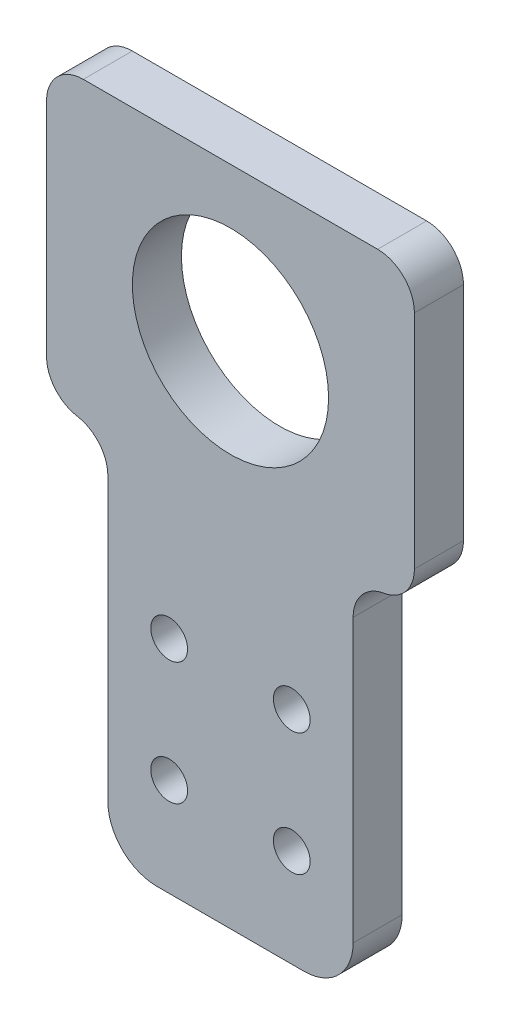
SolidWorks part; units mm, degrees
ref_plane "前视基准面" through (0, 0, 0) normal (0, 0, 1) x (1, 0, 0)
ref_plane "上视基准面" through (0, 0, 0) normal (0, 1, 0) x (1, 0, 0)
ref_plane "右视基准面" through (0, 0, 0) normal (1, 0, 0) x (0, 0, -1)
sketch "草图1" plane through (0, 0, 0) normal (0, 0, 1) x (1, 0, 0)
  line L1 (-10, -15) -> (10, -15)
  line L2 (-10, -15) -> (-10, 15)
  line L3 (-10, 15) -> (10, 15)
  line L4 (10, -15) -> (10, 15)
  line L5 (-10, -15) -> (10, 15) construction
  line L6 (-10, 15) -> (10, -15) construction
  circle A0 centre (-5, 3) radius 1.5
  circle A1 centre (5, 3) radius 1.5
  circle A2 centre (-5, -7) radius 1.5
  circle A3 centre (5, -7) radius 1.5
  point P0 (0, 0)
  dimension "D5" = 3
  dimension "D7" = 3
  dimension "D8" = 3
  dimension "D9" = 3
  dimension "D1" = 10
  dimension "D2" = 20
  dimension "D3" = 30
  dimension "D4" = 10
  dimension "D6" = 10
  dimension "D10" = 5
  dimension "D11" = 8
extrude "凸台-拉伸1" add sketch "草图1" along normal blind 4
sketch "草图2" plane through (0, 15, 0) normal (0, 1, 0) x (1, 0, 0)
  line L1 (-15, 0) -> (15, 0)
  line L2 (-15, 0) -> (-15, -4)
  line L3 (-15, -4) -> (15, -4)
  line L4 (15, 0) -> (15, -4)
  line L5 (-15, 0) -> (15, -4) construction
  line L6 (-15, -4) -> (15, 0) construction
  point P0 (0, -2)
  dimension "D1" = 30
  dimension "D2" = 0
extrude "凸台-拉伸2" add sketch "草图2" along normal blind 24
sketch "草图3" plane through (0, 0, 4) normal (0, 0, 1) x (1, 0, 0)
  line L0 (-15, 39) -> (15, 39) construction
  circle A0 centre (0, 26.5) radius 8
  dimension "D1" = 16
  dimension "D2" = 12.5
fillet "圆角1" radius 3 2 edges at (10, 15, 2) (-10, 15, 2)
extrude "切除-拉伸1" cut sketch "草图3" against normal blind 24
fillet "圆角2" radius 3 4 edges at (15, 15, 2) (15, 39, 2) (-15, 39, 2) (-15, 15, 2)
sketch "草图4" plane through (0, 0, 4) normal (0, 0, 1) x (1, 0, 0)
  circle A0 centre (5, 3) radius 1.5
  circle A1 centre (5, -7) radius 1.5
  circle A2 centre (-5, 3) radius 1.5
  circle A3 centre (-5, -7) radius 1.5
fillet "圆角3" radius 4 1 edges at (-10, -15, 2)
fillet "圆角4" radius 4 1 edges at (10, -15, 2)
